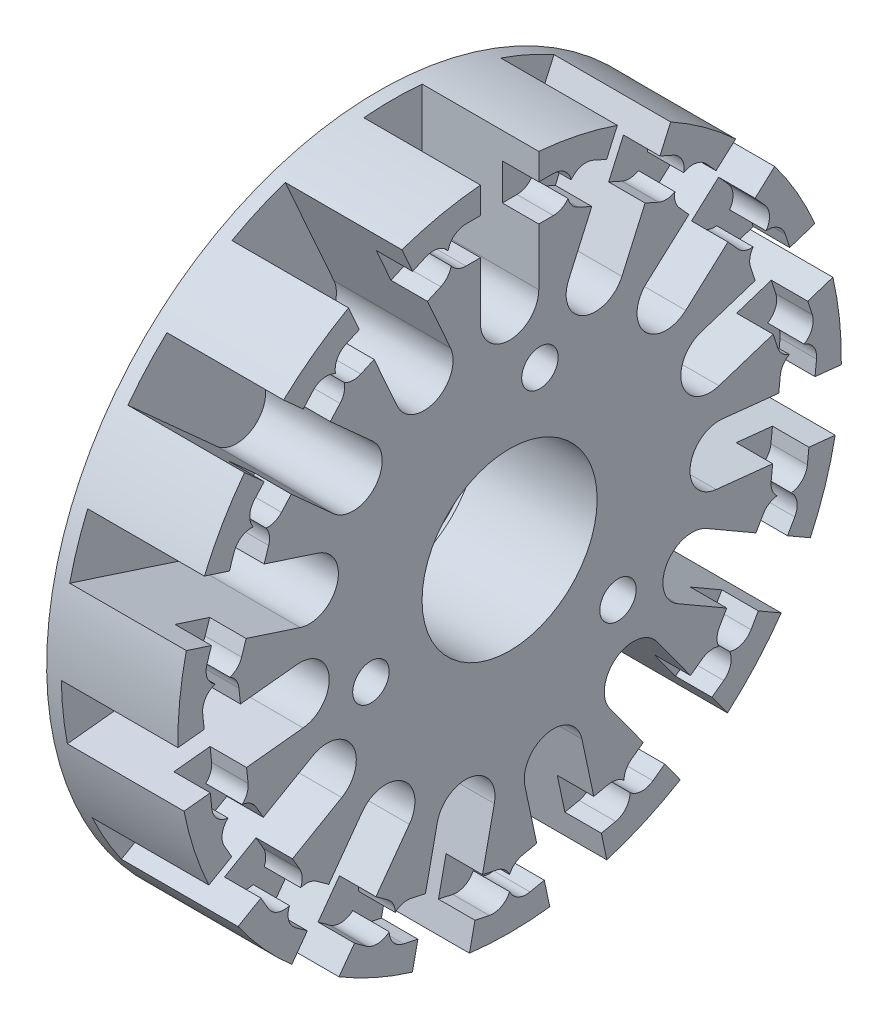
SolidWorks part; units mm, degrees
ref_plane "Front Plane" through (0, 0, 0) normal (0, 0, 1) x (1, 0, 0)
ref_plane "Top Plane" through (0, 0, 0) normal (0, 1, 0) x (1, 0, 0)
ref_plane "Right Plane" through (0, 0, 0) normal (1, 0, 0) x (0, 0, -1)
sketch "Sketch1" plane through (0, 0, 0) normal (1, 0, 0) x (0, 0, -1)
  circle A0 centre (0, 0) radius 22.75
  circle A1 centre (0, 0) radius 6.005
  dimension "D1" = 45.5
  dimension "D2" = 12.01
extrude "Boss-Extrude1" add sketch "Sketch1" along normal blind 9
sketch "Sketch2" plane through (9, 0, 0) normal (1, 0, 0) x (0, 0, -1)
  line L0 (-2, 22.75) -> (2, 22.75)
  line L1 (2, 22.75) -> (2, 14.45)
  line L2 (-2, 14.45) -> (-2, 22.75)
  arc A0 (2, 14.45) -> (-2, 14.45) centre (0, 14.45) cw
  circle A1 centre (0, 0) radius 22.75 construction
  dimension "D1" = 4
  dimension "D2" = 8.3
extrude "Cut-Extrude1" cut sketch "Sketch2" against normal blind 8
sketch "Sketch3" plane through (9, 0, 0) normal (1, 0, 0) x (0, 0, -1)
  line L0 (-3, 19.6) -> (3, 19.6) construction
  line L1 (-3, 20.85) -> (3, 20.85)
  line L2 (-3, 18.35) -> (3, 18.35)
  arc A0 (-3, 20.85) -> (-3, 18.35) centre (-3, 19.6) ccw
  arc A1 (3, 18.35) -> (3, 20.85) centre (3, 19.6) ccw
  arc A2 (-2, 14.45) -> (2, 14.45) centre (0, 14.45) ccw construction
  point P2 (0, 19.6)
  dimension "D1" = 1.25
  dimension "D2" = 5.15
  dimension "D3" = 6
extrude "Cut-Extrude2" cut sketch "Sketch3" against normal blind 2.5
pattern_circular "CirPattern1" count 15 over 360 about axis through (0, 0, 0) along (1, 0, 0) of "Cut-Extrude1", "Cut-Extrude2"
hole_wizard "Tap Drill for M3x0.5 Tap1" positions "Sketch6" profile "Sketch5" hole size "M3x0.5" standard "ANSI Metric"
sketch "Sketch6" plane through (9, 0, 0) normal (1, 0, 0) x (0, 0, -1)
  line L0 (2.0791, 9.7815) -> (0, 0) construction
  line L1 (0, 0) -> (6.005, 0) construction
  circle A2 centre (0, 0) radius 6.005 construction
  point P0 (2.0791, 9.7815)
  dimension "D1" = 78
  dimension "D2" = 10
sketch "Sketch5" plane through (9, 9.7815, -2.0791) normal (0, 1, 0) x (0, 0, -1)
  line L0 (0, 0) -> (0, 7.7511)
  line L1 (0, 7.7511) -> (1.25, 7)
  line L2 (1.25, 7) -> (1.25, 0)
  line L5 (1.25, 0) -> (0, 0)
  line L10 (0, 7.7511) -> (-1.25, 7) construction
  line L11 (0, -6.35) -> (0, 107.95) construction
  dimension "Hole Dia." = 2.5
  dimension "Hole Depth" = 7
  dimension "Drill Angle" = 118
pattern_circular "CirPattern2" count 3 over 360 about axis through (0, 0, 0) along (1, 0, 0) of "Tap Drill for M3x0.5 Tap1"
sketch "Sketch8" plane through (0, 0, 0) normal (-1, 0, 0) x (0, 0, 1)
  circle A0 centre (0, 0) radius 6.8
  dimension "D1" = 13.6
extrude "Cut-Extrude4" cut sketch "Sketch8" against normal blind 0.8
hole_wizard "Tap Drill for M2x0.4 Tap1" positions "Sketch10" profile "Sketch9" hole size "M2x0.4" standard "ANSI Metric"
sketch "Sketch10" plane through (0, 0, 0) normal (-1, 0, 0) x (0, 0, 1)
  line L0 (0, 0) -> (-6.005, 0) construction
  line L1 (-6.005, 0) -> (0, 0) construction
  line L3 (-4.3142, 20.2966) -> (0, 0) construction
  circle A0 centre (0, 0) radius 6.005 construction
  point P0 (-4.3142, 20.2966)
  dimension "D1" = 78
  dimension "D2" = 20.75
sketch "Sketch9" plane through (0, 20.2966, -4.3142) normal (0, 1, 0) x (0, 0, 1)
  line L0 (0, 0) -> (0, 5.9807)
  line L1 (0, 5.9807) -> (0.8, 5.5)
  line L2 (0.8, 5.5) -> (0.8, 0)
  line L5 (0.8, 0) -> (0, 0)
  line L10 (0, 5.9807) -> (-0.8, 5.5) construction
  line L11 (0, -6.35) -> (0, 107.95) construction
  dimension "Hole Dia." = 1.6
  dimension "Hole Depth" = 5.5
  dimension "Drill Angle" = 118
pattern_circular "CirPattern3" count 5 over 360 about axis through (0, 0, 0) along (1, 0, 0) of "Tap Drill for M2x0.4 Tap1"
